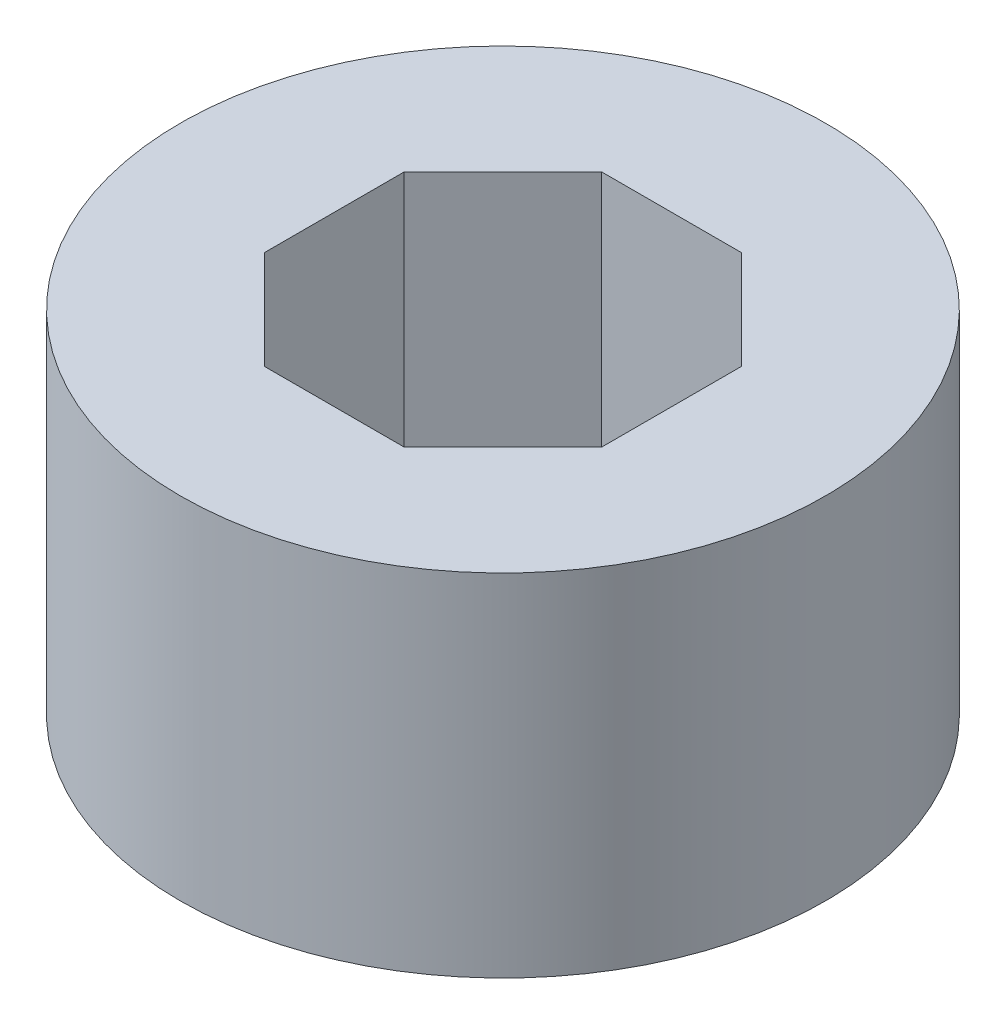
SolidWorks part; units mm, degrees
ref_plane "Front Plane" through (0, 0, 0) normal (0, 0, 1) x (1, 0, 0)
ref_plane "Top Plane" through (0, 0, 0) normal (0, 1, 0) x (1, 0, 0)
ref_plane "Right Plane" through (0, 0, 0) normal (1, 0, 0) x (0, 0, -1)
sketch "Sketch1" plane through (0, 0, 0) normal (0, 1, 0) x (1, 0, 0)
  line L0 (-123.6831, 0) -> (6060.4724, 0) construction
  line L2 (-0.995, 2.4021) -> (-2.4021, 0.995)
  line L3 (-2.4021, 0.995) -> (-2.4021, -0.995)
  line L4 (-2.4021, -0.995) -> (-0.995, -2.4021)
  line L5 (-0.995, -2.4021) -> (0.995, -2.4021)
  line L6 (0.995, -2.4021) -> (2.4021, -0.995)
  line L7 (2.4021, -0.995) -> (2.4021, 0.995)
  line L8 (2.4021, 0.995) -> (0.995, 2.4021)
  line L9 (0.995, 2.4021) -> (-0.995, 2.4021)
  circle A0 centre (0, 0) radius 2.6 construction
  circle A1 centre (0, 0) radius 2.6 construction
  circle A2 centre (0, 0) radius 4.6
  dimension "D1" = 5.2
  dimension "D2" = 2
extrude "Boss-Extrude1" add sketch "Sketch1" along normal blind 5
